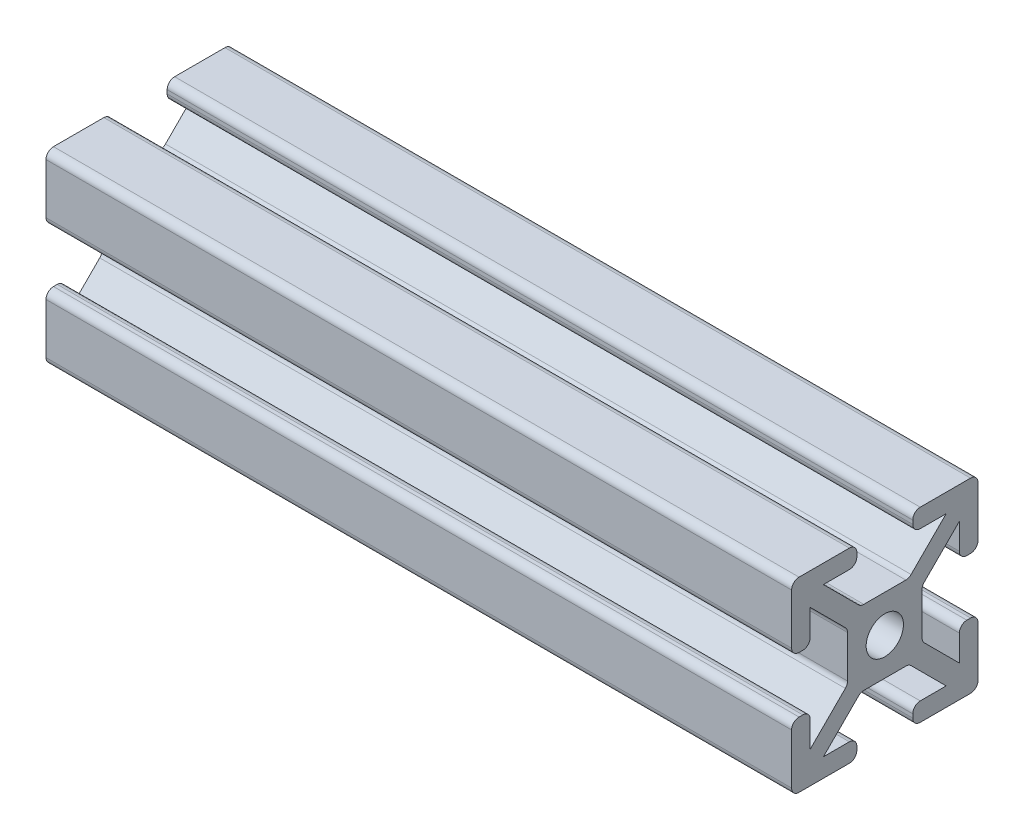
SolidWorks part; units mm, degrees
material "1060 Alloy"
ref_plane "Front Plane" through (0, 0, 0) normal (0, 0, 1) x (1, 0, 0)
ref_plane "Top Plane" through (0, 0, 0) normal (0, 1, 0) x (1, 0, 0)
ref_plane "Right Plane" through (0, 0, 0) normal (1, 0, 0) x (0, 0, -1)
sketch "Sketch1" plane through (0, 0, 0) normal (0, 0, 1) x (1, 0, 0)
  line L0 (-35.5975, 0) -> (44.4025, 0)
  dimension "D1" = 80
other "Profile 4X4(1)"
ref_plane "Plane1" through (-35.5975, 0, 0) normal (1, 0, 0) x (0, 1, 0)
sketch "Sketch11" plane through (-35.5975, 0, 0) normal (1, 0, 0) x (0, 1, 0)
  line L0 (-3, 9.2) -> (-3, 8.8)
  line L1 (-2.2544, 4) -> (2.2544, 4)
  line L2 (-4, 2.2544) -> (-4, -2.2544)
  line L3 (-2.2544, -4) -> (2.2544, -4)
  line L4 (4, 2.2544) -> (4, -2.2544)
  line L7 (-6.5858, 8) -> (-3.8, 8)
  line L8 (-8, 6.5858) -> (-8, 3.8)
  line L9 (-6.5858, -8) -> (-3.8, -8)
  line L10 (8, 6.5858) -> (8, 3.8)
  line L12 (9.7657, -9.7657) -> (10, -10) construction
  line L13 (-9.2, 10) -> (-3.8, 10)
  line L14 (-10, 9.2) -> (-10, 3.8)
  line L15 (-9.2, -10) -> (-3.8, -10)
  line L16 (10, 9.2) -> (10, 3.8)
  line L17 (-10, 10) -> (-9.7657, 9.7657) construction
  line L18 (-10, -10) -> (-9.7657, -9.7657) construction
  line L21 (3, 9.2) -> (3, 8.8)
  line L22 (3, -9.2) -> (3, -8.8)
  line L23 (-3, -9.2) -> (-3, -8.8)
  line L24 (3.8, 10) -> (9.2, 10)
  line L25 (3.8, 8) -> (6.5858, 8)
  line L26 (-9.2, 3) -> (-8.8, 3)
  line L27 (9.2, 3) -> (8.8, 3)
  line L28 (9.2, -3) -> (8.8, -3)
  line L29 (-9.2, -3) -> (-8.8, -3)
  line L30 (-10, -3.8) -> (-10, -9.2)
  line L31 (-8, -3.8) -> (-8, -6.5858)
  line L32 (8, -3.8) -> (8, -6.5858)
  line L33 (10, -3.8) -> (10, -9.2)
  line L34 (3.8, -8) -> (6.5858, -8)
  line L35 (3.8, -10) -> (9.2, -10)
  line L36 (6.5858, 8) -> (2.8201, 4.2343)
  line L37 (8, 6.5858) -> (4.2343, 2.8201)
  line L38 (8, -6.5858) -> (4.2343, -2.8201)
  line L39 (6.5858, -8) -> (2.8201, -4.2343)
  line L40 (-6.5858, -8) -> (-2.8201, -4.2343)
  line L41 (-8, -6.5858) -> (-4.2343, -2.8201)
  line L42 (-8, 6.5858) -> (-4.2343, 2.8201)
  line L43 (-6.5858, 8) -> (-2.8201, 4.2343)
  line L47 (9.7657, 9.7657) -> (10, 10) construction
  circle A0 centre (0, 0) radius 2
  arc A1 (9.2, -3) -> (10, -3.8) centre (9.2, -3.8) cw
  arc A2 (8.8, -3) -> (8, -3.8) centre (8.8, -3.8) ccw
  arc A3 (3, -9.2) -> (3.8, -10) centre (3.8, -9.2) ccw
  arc A4 (3, -8.8) -> (3.8, -8) centre (3.8, -8.8) cw
  arc A5 (-3, -9.2) -> (-3.8, -10) centre (-3.8, -9.2) cw
  arc A6 (-3, -8.8) -> (-3.8, -8) centre (-3.8, -8.8) ccw
  arc A7 (-8.8, -3) -> (-8, -3.8) centre (-8.8, -3.8) cw
  arc A8 (-9.2, -3) -> (-10, -3.8) centre (-9.2, -3.8) ccw
  arc A9 (-10, -9.2) -> (-9.2, -10) centre (-9.2, -9.2) ccw
  arc A10 (9.2, -10) -> (10, -9.2) centre (9.2, -9.2) ccw
  arc A11 (9.2, 10) -> (10, 9.2) centre (9.2, 9.2) cw
  arc A12 (-9.2, 10) -> (-10, 9.2) centre (-9.2, 9.2) ccw
  arc A13 (9.2, 3) -> (10, 3.8) centre (9.2, 3.8) ccw
  arc A14 (8.8, 3) -> (8, 3.8) centre (8.8, 3.8) cw
  arc A15 (3, 9.2) -> (3.8, 10) centre (3.8, 9.2) cw
  arc A16 (3, 8.8) -> (3.8, 8) centre (3.8, 8.8) ccw
  arc A17 (-3, 9.2) -> (-3.8, 10) centre (-3.8, 9.2) ccw
  arc A18 (-3, 8.8) -> (-3.8, 8) centre (-3.8, 8.8) cw
  arc A19 (-8.8, 3) -> (-8, 3.8) centre (-8.8, 3.8) ccw
  arc A20 (-9.2, 3) -> (-10, 3.8) centre (-9.2, 3.8) cw
  arc A21 (-2.8201, 4.2343) -> (-2.2544, 4) centre (-2.2544, 4.8) ccw
  arc A22 (4.2343, 2.8201) -> (4, 2.2544) centre (4.8, 2.2544) ccw
  arc A23 (2.8201, 4.2343) -> (2.2544, 4) centre (2.2544, 4.8) cw
  arc A24 (4.2343, -2.8201) -> (4, -2.2544) centre (4.8, -2.2544) cw
  arc A25 (2.8201, -4.2343) -> (2.2544, -4) centre (2.2544, -4.8) ccw
  arc A26 (-2.8201, -4.2343) -> (-2.2544, -4) centre (-2.2544, -4.8) cw
  arc A27 (-4.2343, -2.8201) -> (-4, -2.2544) centre (-4.8, -2.2544) ccw
  arc A28 (-4.2343, 2.8201) -> (-4, 2.2544) centre (-4.8, 2.2544) cw
  point P7 (0, 0)
  point P10 (-2.5858, 4)
  point P53 (10, -3)
  point P56 (8, -3)
  point P59 (3, -10)
  point P62 (3, -8)
  point P65 (-3, -10)
  point P68 (-3, -8)
  point P71 (-8, -3)
  point P74 (-10, -3)
  point P89 (10, 3)
  point P92 (8, 3)
  point P95 (3, 10)
  point P98 (3, 8)
  point P101 (-3, 10)
  point P104 (-3, 8)
  point P107 (-8, 3)
  point P110 (-10, 3)
  point P116 (4, 2.5858)
  point P119 (2.5858, 4)
  point P122 (4, -2.5858)
  point P125 (2.5858, -4)
  point P128 (-2.5858, -4)
  point P131 (-4, -2.5858)
  point P134 (-4, 2.5858)
  dimension "D3" = 4
  dimension "D11" = 0.8
  dimension "D12" = 0.8
  dimension "D2" = 0.8
  dimension "D4" = 20
  dimension "D6" = 20
  dimension "D8" = 7
  dimension "D9" = 7
